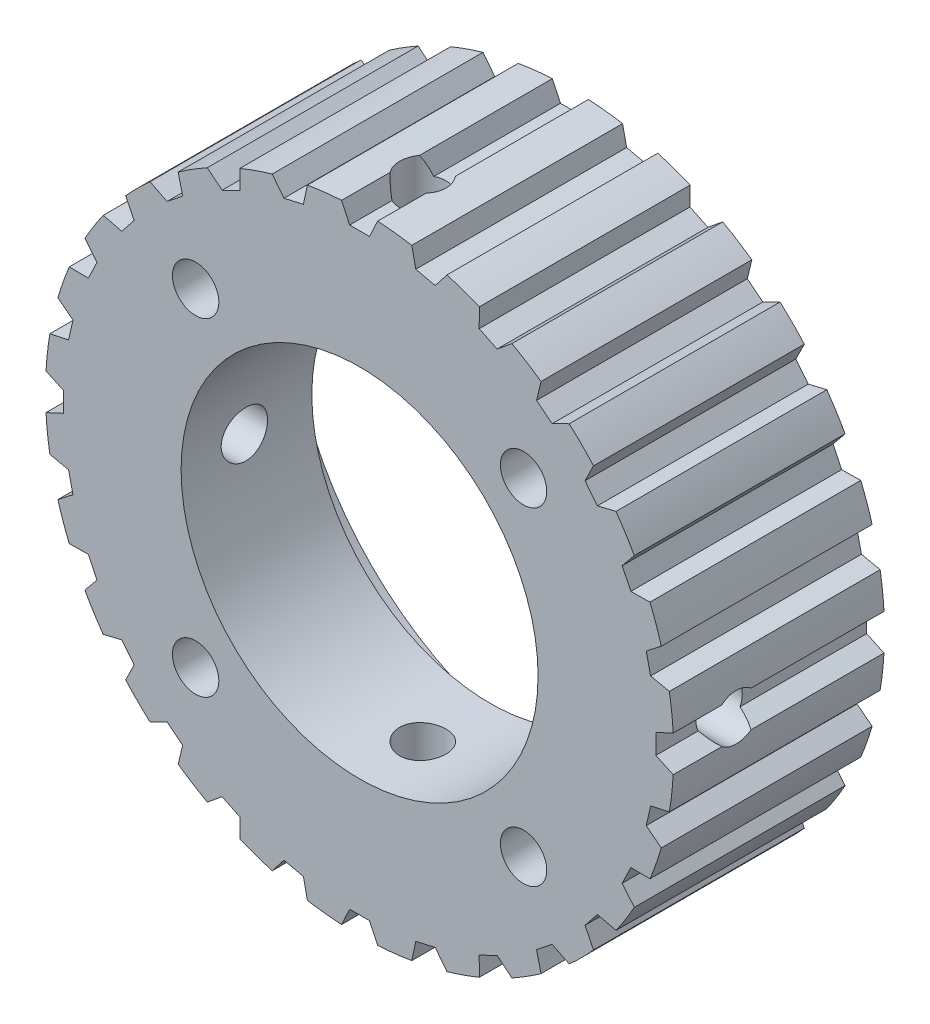
SolidWorks part; units mm, degrees
ref_plane "Front Plane" through (0, 0, 0) normal (0, 0, 1) x (1, 0, 0)
ref_plane "Top Plane" through (0, 0, 0) normal (0, 1, 0) x (1, 0, 0)
ref_plane "Right Plane" through (0, 0, 0) normal (1, 0, 0) x (0, 0, -1)
sketch "Sketch1" plane through (0, 0, 0) normal (0, 0, 1) x (1, 0, 0)
  circle A0 centre (0, 0) radius 22.35
  dimension "D1" = 44.7
extrude "Boss-Extrude1" add sketch "Sketch1" along normal blind 15
sketch "Sketch2" plane through (0, 0, 0) normal (0, 0, -1) x (-1, 0, 0)
  line L0 (0, 0) -> (0, 23.9261) construction
  line L1 (-0.7078, 21.08) -> (0.7078, 21.08)
  line L2 (0.7078, 21.08) -> (1.3, 22.35)
  line L3 (1.3, 22.35) -> (-1.3, 22.35)
  line L4 (-1.3, 22.35) -> (-0.7078, 21.08)
  line L5 (4.0007, 20.709) -> (5.3808, 20.394)
  line L6 (5.3808, 20.394) -> (6.2407, 21.5004)
  line L7 (6.2407, 21.5004) -> (3.7059, 22.0789)
  line L8 (3.7059, 22.0789) -> (4.0007, 20.709)
  line L9 (8.5086, 19.2995) -> (9.784, 18.6853)
  line L10 (9.784, 18.6853) -> (10.8686, 19.5726)
  line L11 (10.8686, 19.5726) -> (8.526, 20.7007)
  line L12 (8.526, 20.7007) -> (8.5086, 19.2995)
  line L13 (12.5898, 16.9223) -> (13.6965, 16.0397)
  line L14 (13.6965, 16.0397) -> (14.9514, 16.6634)
  line L15 (14.9514, 16.6634) -> (12.9186, 18.2845)
  line L16 (12.9186, 18.2845) -> (12.5898, 16.9223)
  line L17 (16.0397, 13.6965) -> (16.9223, 12.5898)
  line L18 (16.9223, 12.5898) -> (18.2845, 12.9186)
  line L19 (18.2845, 12.9186) -> (16.6634, 14.9514)
  line L20 (16.6634, 14.9514) -> (16.0397, 13.6965)
  line L21 (18.6853, 9.784) -> (19.2995, 8.5086)
  line L22 (19.2995, 8.5086) -> (20.7007, 8.526)
  line L23 (20.7007, 8.526) -> (19.5726, 10.8686)
  line L24 (19.5726, 10.8686) -> (18.6853, 9.784)
  line L25 (20.394, 5.3808) -> (20.709, 4.0007)
  line L26 (20.709, 4.0007) -> (22.0789, 3.7059)
  line L27 (22.0789, 3.7059) -> (21.5004, 6.2407)
  line L28 (21.5004, 6.2407) -> (20.394, 5.3808)
  line L29 (21.08, 0.7078) -> (21.08, -0.7078)
  line L30 (21.08, -0.7078) -> (22.35, -1.3)
  line L31 (22.35, -1.3) -> (22.35, 1.3)
  line L32 (22.35, 1.3) -> (21.08, 0.7078)
  line L33 (20.709, -4.0007) -> (20.394, -5.3808)
  line L34 (20.394, -5.3808) -> (21.5004, -6.2407)
  line L35 (21.5004, -6.2407) -> (22.0789, -3.7059)
  line L36 (22.0789, -3.7059) -> (20.709, -4.0007)
  line L37 (19.2995, -8.5086) -> (18.6853, -9.784)
  line L38 (18.6853, -9.784) -> (19.5726, -10.8686)
  line L39 (19.5726, -10.8686) -> (20.7007, -8.526)
  line L40 (20.7007, -8.526) -> (19.2995, -8.5086)
  line L41 (16.9223, -12.5898) -> (16.0397, -13.6965)
  line L42 (16.0397, -13.6965) -> (16.6634, -14.9514)
  line L43 (16.6634, -14.9514) -> (18.2845, -12.9186)
  line L44 (18.2845, -12.9186) -> (16.9223, -12.5898)
  line L45 (13.6965, -16.0397) -> (12.5898, -16.9223)
  line L46 (12.5898, -16.9223) -> (12.9186, -18.2845)
  line L47 (12.9186, -18.2845) -> (14.9514, -16.6634)
  line L48 (14.9514, -16.6634) -> (13.6965, -16.0397)
  line L49 (9.784, -18.6853) -> (8.5086, -19.2995)
  line L50 (8.5086, -19.2995) -> (8.526, -20.7007)
  line L51 (8.526, -20.7007) -> (10.8686, -19.5726)
  line L52 (10.8686, -19.5726) -> (9.784, -18.6853)
  line L53 (5.3808, -20.394) -> (4.0007, -20.709)
  line L54 (4.0007, -20.709) -> (3.7059, -22.0789)
  line L55 (3.7059, -22.0789) -> (6.2407, -21.5004)
  line L56 (6.2407, -21.5004) -> (5.3808, -20.394)
  line L57 (0.7078, -21.08) -> (-0.7078, -21.08)
  line L58 (-0.7078, -21.08) -> (-1.3, -22.35)
  line L59 (-1.3, -22.35) -> (1.3, -22.35)
  line L60 (1.3, -22.35) -> (0.7078, -21.08)
  line L61 (-4.0007, -20.709) -> (-5.3808, -20.394)
  line L62 (-5.3808, -20.394) -> (-6.2407, -21.5004)
  line L63 (-6.2407, -21.5004) -> (-3.7059, -22.0789)
  line L64 (-3.7059, -22.0789) -> (-4.0007, -20.709)
  line L65 (-8.5086, -19.2995) -> (-9.784, -18.6853)
  line L66 (-9.784, -18.6853) -> (-10.8686, -19.5726)
  line L67 (-10.8686, -19.5726) -> (-8.526, -20.7007)
  line L68 (-8.526, -20.7007) -> (-8.5086, -19.2995)
  line L69 (-12.5898, -16.9223) -> (-13.6965, -16.0397)
  line L70 (-13.6965, -16.0397) -> (-14.9514, -16.6634)
  line L71 (-14.9514, -16.6634) -> (-12.9186, -18.2845)
  line L72 (-12.9186, -18.2845) -> (-12.5898, -16.9223)
  line L73 (-16.0397, -13.6965) -> (-16.9223, -12.5898)
  line L74 (-16.9223, -12.5898) -> (-18.2845, -12.9186)
  line L75 (-18.2845, -12.9186) -> (-16.6634, -14.9514)
  line L76 (-16.6634, -14.9514) -> (-16.0397, -13.6965)
  line L77 (-18.6853, -9.784) -> (-19.2995, -8.5086)
  line L78 (-19.2995, -8.5086) -> (-20.7007, -8.526)
  line L79 (-20.7007, -8.526) -> (-19.5726, -10.8686)
  line L80 (-19.5726, -10.8686) -> (-18.6853, -9.784)
  line L81 (-20.394, -5.3808) -> (-20.709, -4.0007)
  line L82 (-20.709, -4.0007) -> (-22.0789, -3.7059)
  line L83 (-22.0789, -3.7059) -> (-21.5004, -6.2407)
  line L84 (-21.5004, -6.2407) -> (-20.394, -5.3808)
  line L85 (-21.08, -0.7078) -> (-21.08, 0.7078)
  line L86 (-21.08, 0.7078) -> (-22.35, 1.3)
  line L87 (-22.35, 1.3) -> (-22.35, -1.3)
  line L88 (-22.35, -1.3) -> (-21.08, -0.7078)
  line L89 (-20.709, 4.0007) -> (-20.394, 5.3808)
  line L90 (-20.394, 5.3808) -> (-21.5004, 6.2407)
  line L91 (-21.5004, 6.2407) -> (-22.0789, 3.7059)
  line L92 (-22.0789, 3.7059) -> (-20.709, 4.0007)
  line L93 (-19.2995, 8.5086) -> (-18.6853, 9.784)
  line L94 (-18.6853, 9.784) -> (-19.5726, 10.8686)
  line L95 (-19.5726, 10.8686) -> (-20.7007, 8.526)
  line L96 (-20.7007, 8.526) -> (-19.2995, 8.5086)
  line L97 (-16.9223, 12.5898) -> (-16.0397, 13.6965)
  line L98 (-16.0397, 13.6965) -> (-16.6634, 14.9514)
  line L99 (-16.6634, 14.9514) -> (-18.2845, 12.9186)
  line L100 (-18.2845, 12.9186) -> (-16.9223, 12.5898)
  line L101 (-13.6965, 16.0397) -> (-12.5898, 16.9223)
  line L102 (-12.5898, 16.9223) -> (-12.9186, 18.2845)
  line L103 (-12.9186, 18.2845) -> (-14.9514, 16.6634)
  line L104 (-14.9514, 16.6634) -> (-13.6965, 16.0397)
  line L105 (-9.784, 18.6853) -> (-8.5086, 19.2995)
  line L106 (-8.5086, 19.2995) -> (-8.526, 20.7007)
  line L107 (-8.526, 20.7007) -> (-10.8686, 19.5726)
  line L108 (-10.8686, 19.5726) -> (-9.784, 18.6853)
  line L109 (-5.3808, 20.394) -> (-4.0007, 20.709)
  line L110 (-4.0007, 20.709) -> (-3.7059, 22.0789)
  line L111 (-3.7059, 22.0789) -> (-6.2407, 21.5004)
  line L112 (-6.2407, 21.5004) -> (-5.3808, 20.394)
  circle A2 centre (0, 0) radius 22.35 construction
  point P10 (0, 22.35)
  point P11 (4.9733, 21.7896)
  point P119 (0, 0)
  point P127 (0.7136, -0.075)
  dimension "D3" = 1.27
  dimension "D1" = 25
  dimension "D2" = 25
  dimension "D4" = 2.6
  dimension "D5" = 1.3
  dimension "D7" = 5.0048
  dimension "D6" = 28
extrude "Cut-Extrude1" cut sketch "Sketch2" against normal through all
sketch "Sketch3" plane through (0, 0, 0) normal (0, 0, -1) x (-1, 0, 0)
  circle A0 centre (0, 0) radius 12.7
  dimension "D1" = 25.4
extrude "Cut-Extrude2" cut sketch "Sketch3" against normal through all
sketch "Sketch4" plane through (0, 0, 0) normal (0, 0, -1) x (-1, 0, 0)
  circle A0 centre (0, 0) radius 20
  dimension "D1" = 40
extrude "Cut-Extrude3" cut sketch "Sketch4" against normal blind 5.7
sketch "Sketch5" plane through (0, 0, 5.7) normal (0, 0, -1) x (-1, 0, 0)
  line L0 (0, 0) -> (0, 21.08) construction
  line L1 (-0.7078, 21.08) -> (0.7078, 21.08) construction
  line L2 (0, 0) -> (-11.6673, 11.6673) construction
  circle A0 centre (0, 0) radius 16.5 construction
  circle A1 centre (-11.6673, 11.6673) radius 1.65
  circle A2 centre (0, 0) radius 16.5 construction
  circle A3 centre (11.6673, 11.6673) radius 1.65
  circle A4 centre (0, 0) radius 16.5 construction
  circle A5 centre (11.6673, -11.6673) radius 1.65
  circle A6 centre (0, 0) radius 16.5 construction
  circle A7 centre (-11.6673, -11.6673) radius 1.65
  point P17 (0, 0)
  point P21 (0, 0)
  dimension "D1" = 33
  dimension "D2" = 3.3
  dimension "D4" = 45
  dimension "D3" = 4
extrude "Cut-Extrude4" cut sketch "Sketch5" against normal through all
sketch "Sketch6" plane through (0, 0, 0) normal (0, 1, 0) x (1, 0, 0)
  line L0 (-22.3132, -7.5) -> (22.3132, -7.5) construction
  line L1 (-22.3132, 0) -> (-22.3132, -15) construction
  line L2 (22.3132, -15) -> (22.3132, 0) construction
  line L3 (0, -10.5) -> (0, -15) construction
  line L4 (0.7078, -15) -> (-0.7078, -15) construction
  line L5 (1.2828, -15) -> (3.7145, -15) construction
  circle A0 centre (0, -10.5) radius 1.65
  dimension "D1" = 3.3
  dimension "D2" = 4.5
extrude "Cut-Extrude5" cut sketch "Sketch6" against normal through all and the other way through all
sketch "Sketch7" plane through (0, 0, 0) normal (1, 0, 0) x (0, 0, -1)
  line L0 (-7.5, 22.0392) -> (-7.5, -22.0392) construction
  line L1 (-15, 22.0392) -> (0, 22.0392) construction
  line L2 (0, -22.0392) -> (-15, -22.0392) construction
  line L3 (-10.5, 0) -> (-15, 0) construction
  line L4 (-15, -0.7078) -> (-15, 0.7078) construction
  circle A0 centre (-10.5, 0) radius 1.65
  dimension "D1" = 3.3
  dimension "D2" = 4.5
extrude "Cut-Extrude6" cut sketch "Sketch7" against normal through all and the other way through all
